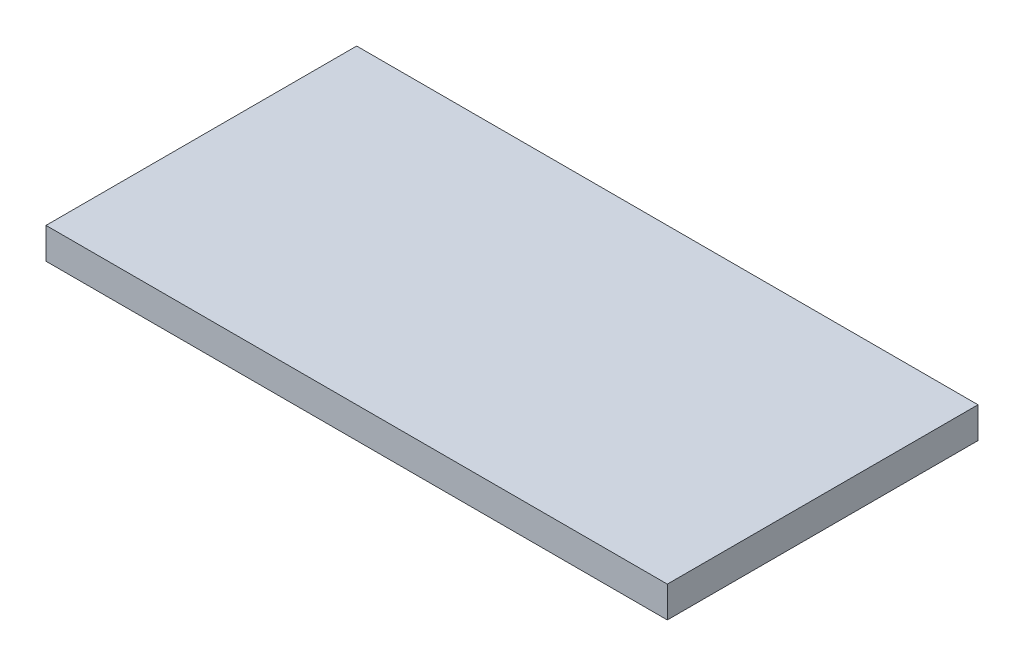
SolidWorks part; units mm, degrees
ref_plane "Front Plane" through (0, 0, 0) normal (0, 0, 1) x (1, 0, 0)
ref_plane "Top Plane" through (0, 0, 0) normal (0, 1, 0) x (1, 0, 0)
ref_plane "Right Plane" through (0, 0, 0) normal (1, 0, 0) x (0, 0, -1)
sketch "Sketch1" plane through (0, 0, 0) normal (0, 1, 0) x (1, 0, 0)
  line L1 (-10, 5) -> (10, 5)
  line L2 (-10, 5) -> (-10, -5)
  line L3 (-10, -5) -> (10, -5)
  line L4 (10, 5) -> (10, -5)
  line L5 (-10, 5) -> (10, -5) construction
  line L6 (-10, -5) -> (10, 5) construction
  point P0 (0, 0)
  dimension "D1" = 10
  dimension "D2" = 20
extrude "Boss-Extrude1" add sketch "Sketch1" along normal blind 1
